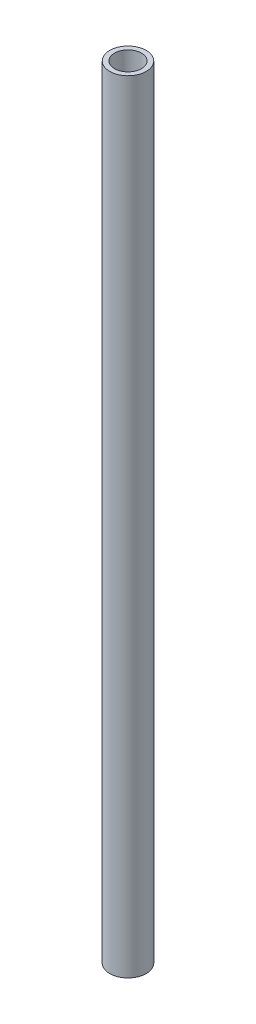
SolidWorks part; units mm, degrees
ref_plane "Front Plane" through (0, 0, 0) normal (0, 0, 1) x (1, 0, 0)
ref_plane "Top Plane" through (0, 0, 0) normal (0, 1, 0) x (1, 0, 0)
ref_plane "Right Plane" through (0, 0, 0) normal (1, 0, 0) x (0, 0, -1)
sketch "Sketch1" plane through (0, 0, 0) normal (0, 1, 0) x (1, 0, 0)
  circle A0 centre (0, 0) radius 7.8994
  circle A1 centre (0, 0) radius 10.668
  dimension "D1" = 15.7988
  dimension "D2" = 21.336
extrude "Boss-Extrude1" add sketch "Sketch1" along normal blind 457.2
